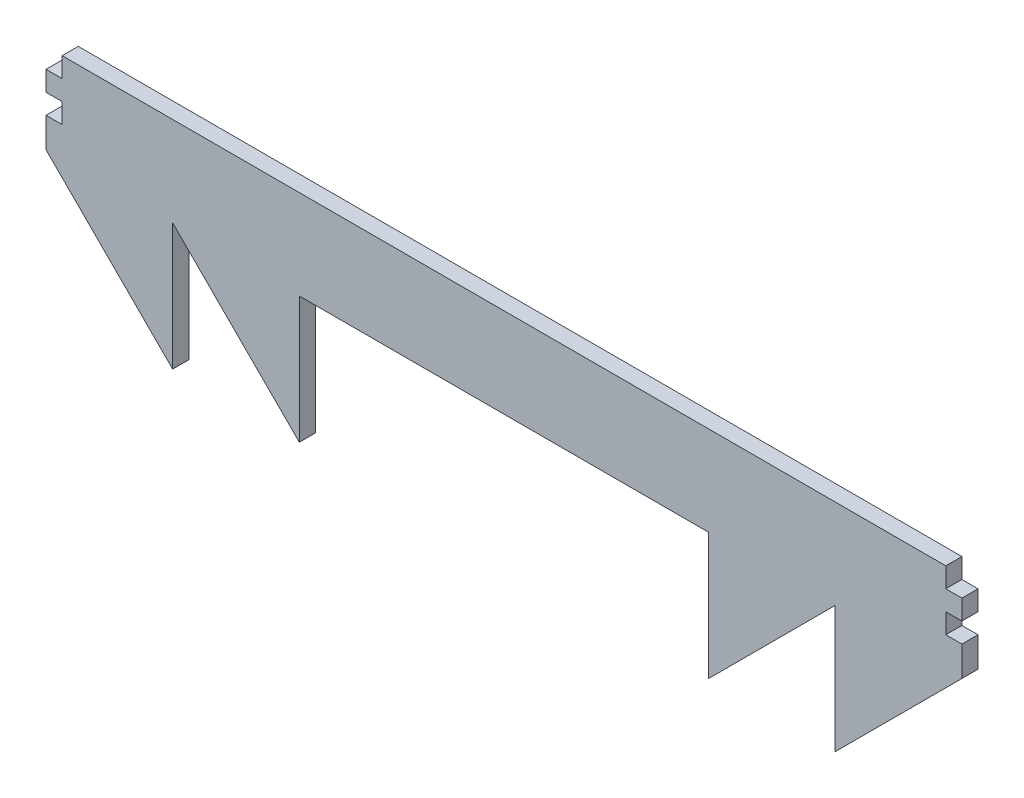
SolidWorks part; units mm, degrees
ref_plane "Ön Düzlem" through (0, 0, 0) normal (0, 0, 1) x (1, 0, 0)
ref_plane "Üst Düzlem" through (0, 0, 0) normal (0, 1, 0) x (1, 0, 0)
ref_plane "Sağ Düzlem" through (0, 0, 0) normal (1, 0, 0) x (0, 0, -1)
sketch "Sketch1" plane through (0, 0, 0) normal (0, 0, 1) x (1, 0, 0)
  line L0 (-76.7, -1.6667) -> (-76.7, 1.6667)
  line L5 (76.7, 1.6667) -> (74, 1.6667)
  line L6 (-74, -1.6667) -> (-74, -5)
  line L8 (76.7, -1.6667) -> (76.7, 1.6667)
  line L10 (-76.7, 1.6667) -> (-74, 1.6667)
  line L11 (-74, 1.6667) -> (-74, 5)
  line L12 (-76.7, -1.6667) -> (-74, -1.6667)
  line L13 (74, 1.6667) -> (74, 5)
  line L14 (76.7, -1.6667) -> (74, -1.6667)
  line L15 (74, -1.6667) -> (74, -5)
  line L16 (-74, -5) -> (-76.7, -5)
  line L17 (-76.7, -5) -> (-76.7, -10)
  line L19 (76.7, -10) -> (76.7, -5)
  line L20 (76.7, -5) -> (74, -5)
  line L25 (76.7, -10) -> (55.4868, -31.2132)
  line L26 (55.4868, -31.2132) -> (55.4868, -10)
  line L28 (34.2736, -31.2132) -> (34.2736, -10)
  line L29 (55.4868, -10) -> (34.2736, -31.2132)
  line L36 (-55.4868, -10) -> (-34.2736, -31.2132)
  line L37 (-34.2736, -31.2132) -> (-34.2736, -10)
  line L39 (-76.7, -10) -> (-55.4868, -31.2132)
  line L40 (-55.4868, -31.2132) -> (-55.4868, -10)
  line L42 (-34.2736, -10) -> (34.2736, -10)
  line L43 (74, 5) -> (-74, 5)
  point P0 (0, 0)
extrude "Boss-Extrude1" add sketch "Sketch1" along normal blind 2.7
